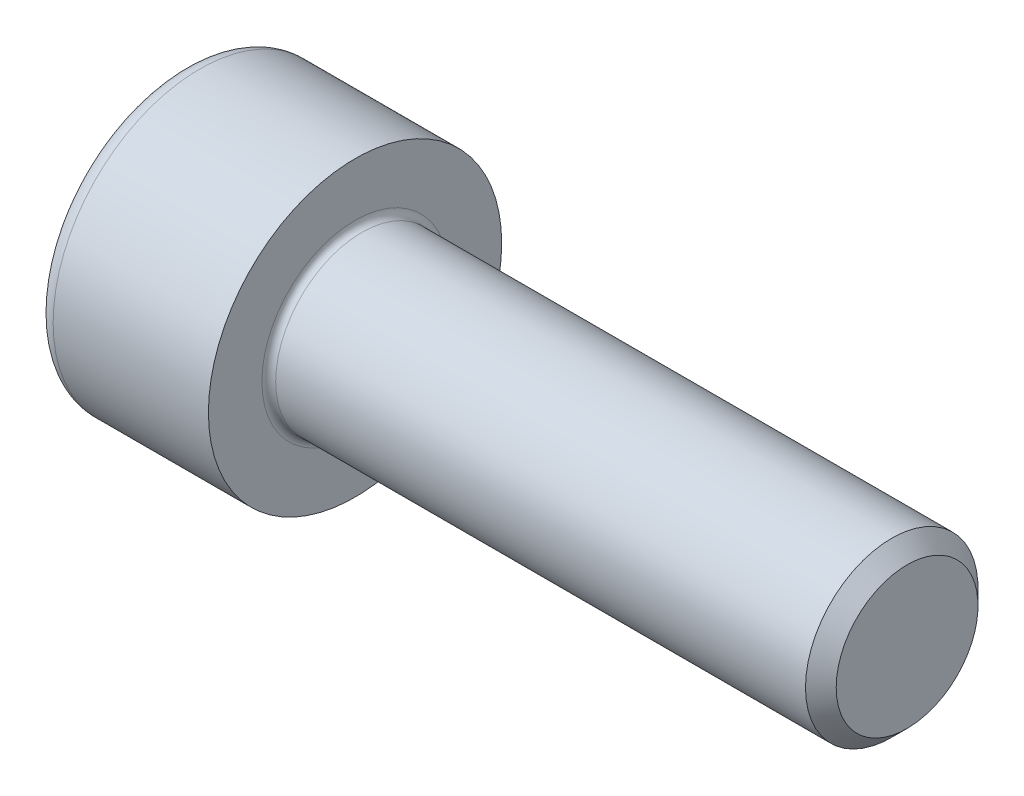
SolidWorks part; units mm, degrees
ref_plane "Plane1" through (0, 0, 0) normal (0, 0, 1) x (1, 0, 0)
ref_plane "Plane2" through (0, 0, 0) normal (0, 1, 0) x (1, 0, 0)
ref_plane "Plane3" through (0, 0, 0) normal (1, 0, 0) x (0, 0, -1)
sketch "BodySke" plane through (0, 0, 0) normal (0, 0, 1) x (1, 0, 0)
  line L0 (0, 0) -> (0, 4.25)
  line L1 (0, 4.25) -> (5, 4.25)
  line L2 (5, 4.25) -> (5, 2.5)
  line L3 (5, 2.5) -> (20.555, 2.5)
  line L4 (21, 2.055) -> (21, 0)
  line L5 (21, 0) -> (0, 0)
  line L6 (-31.75, 0) -> (127, 0) construction
  line L8 (21, 2.055) -> (20.555, 2.5)
  line L10 (21, -2.055) -> (20.555, -2.5) construction
  line L11 (5.8, 9.525) -> (5.8, 3.175) construction
  line L12 (5, 9.525) -> (5, 3.175) construction
  line L13 (-39, 9.525) -> (-39, 3.175) construction
  dimension "Diameter" = 5
  dimension "Head_ht" = 5
  dimension "Length" = 16
  dimension "Body_ch_ang" = 45
  dimension "Head_dia" = 8.5
  dimension "Minor_dia" = 4.11
  dimension "Advance" = 0.8
  dimension "Thread_nom" = 16
  dimension "Thread_length" = 60
revolve "Base-Revolve" add sketch "BodySke"
cosmetic thread "ThreadCosmetic" [suppressed]
fillet "Fillet1" radius 0.2 1 edges at (5, 0, 2.5)
fillet "Fillet2" radius 0.5 1 edges at (0, 0, 4.25)
sketch "Sketch2" plane through (0, 0, 0) normal (0, 0, 1) x (1, 0, 0)
  line L0 (0, 2.01) -> (2.5, 2.01)
  line L1 (2.5, 2.01) -> (3.6605, 0)
  line L2 (-31.75, 0) -> (127, 0) construction
  line L3 (3.6605, 0) -> (0, 0)
  line L4 (0, 0) -> (0, 2.01)
  line L6 (0, 0) -> (47.625, 0) construction
  dimension "D1" = 2.01
  dimension "D2" = 60
  dimension "Depth" = 2.5
revolve "Hex-PreBroach" cut sketch "Sketch2" angle 360 about L6
sketch "Sketch3" plane through (0, 0, 0) normal (-1, 0, 0) x (0, 0.5, 0.866)
  line L0 (1.1605, 2.01) -> (-1.1605, 2.01)
  line L1 (-1.1605, 2.01) -> (-2.3209, 0)
  line L2 (1.1605, 2.01) -> (2.3209, 0)
  line L3 (1.1605, -2.01) -> (2.3209, 0)
  line L4 (1.1605, -2.01) -> (-1.1605, -2.01)
  line L5 (-1.1605, -2.01) -> (-2.3209, 0)
  dimension "D1" = 2.01
  dimension "D2" = 2.01
  dimension "Hex_size" = 4.02
extrude "Hex" cut sketch "Sketch3" against normal blind 2.5
sketch "ThdSchSke" plane through (0, 0, 0) normal (0, 0, 1) x (1, 0, 0)
  line L0 (7.4, -2.055) -> (7.0884, -2.5)
  line L1 (7.4, -2.055) -> (7.7116, -2.5)
  line L2 (7.7116, -2.5) -> (7.7116, -3.125)
  line L3 (-3.175, 0) -> (5.1513, 0) construction
  line L4 (0, 3.75) -> (0, -3.75) construction
  line L5 (7.7116, -3.125) -> (7.0884, -3.125)
  line L6 (7.0884, -3.125) -> (7.0884, -2.5)
  dimension "Thread_minor" = 4.11
  dimension "Diameter" = 5
  dimension "Start" = 7.4
  dimension "SideAngle" = 55
  dimension "VeeAngle" = 70
  dimension "Overcut" = 6.25
revolve "ThreadSchematic" [suppressed] cut sketch "ThdSchSke" angle 360 about L3
pattern_linear "ThdSchPat" [suppressed]
equation "\"D2@Sketch3\" = \"Hex_size@Sketch3\" / 2"
equation "\"D1@Sketch3\" = \"Hex_size@Sketch3\" / 2"
equation "\"D1@Sketch2\" = \"Hex_size@Sketch3\" / 2"
equation "\"Thread_minor@ThreadCosmetic\"  =  \"Minor_dia@BodySke\""
equation "\"Depth@Sketch2\" =  \"Key_eng@Hex\""
equation "\"Thread_length@ThreadCosmetic\" = ((sgn( (\"Length@BodySke\" - \"Advance@BodySke\" * 3.0) - \"Thread_nom@BodySke\" )-1)*( (\"Length@BodySke\" - \"Advance@BodySke\" * 3.0) - \"Thread_nom@BodySke\" ))/-2+ \"Thread_nom@BodySke\""
equation "\"Thread_minor@ThdSchSke\" = \"Minor_dia@BodySke\""
equation "\"Diameter@ThdSchSke\" = \"Diameter@BodySke\""
equation "\"Overcut@ThdSchSke\" = \"Diameter@BodySke\" * 1.25"
equation "\"Start@ThdSchSke\" = \"Head_ht@BodySke\" + \"Length@BodySke\" - \"Thread_length@ThreadCosmetic\"  '---Non-countersunk---"
equation "\"Num_threads@ThdSchPat\" = int( \"Thread_length@ThreadCosmetic\" / \"Advance@BodySke\" + 0.999 )  + 1"
equation "\"Advance@ThdSchPat\" = \"Thread_length@ThreadCosmetic\" /  (\"Num_threads@ThdSchPat\" - 1) 'relax it"
equation "\"Num_threads@ThdSchPat\" = \"Num_threads@ThdSchPat\" - sgn( \"Num_threads@ThdSchPat\" - 1) '---chamfered tips only---"
